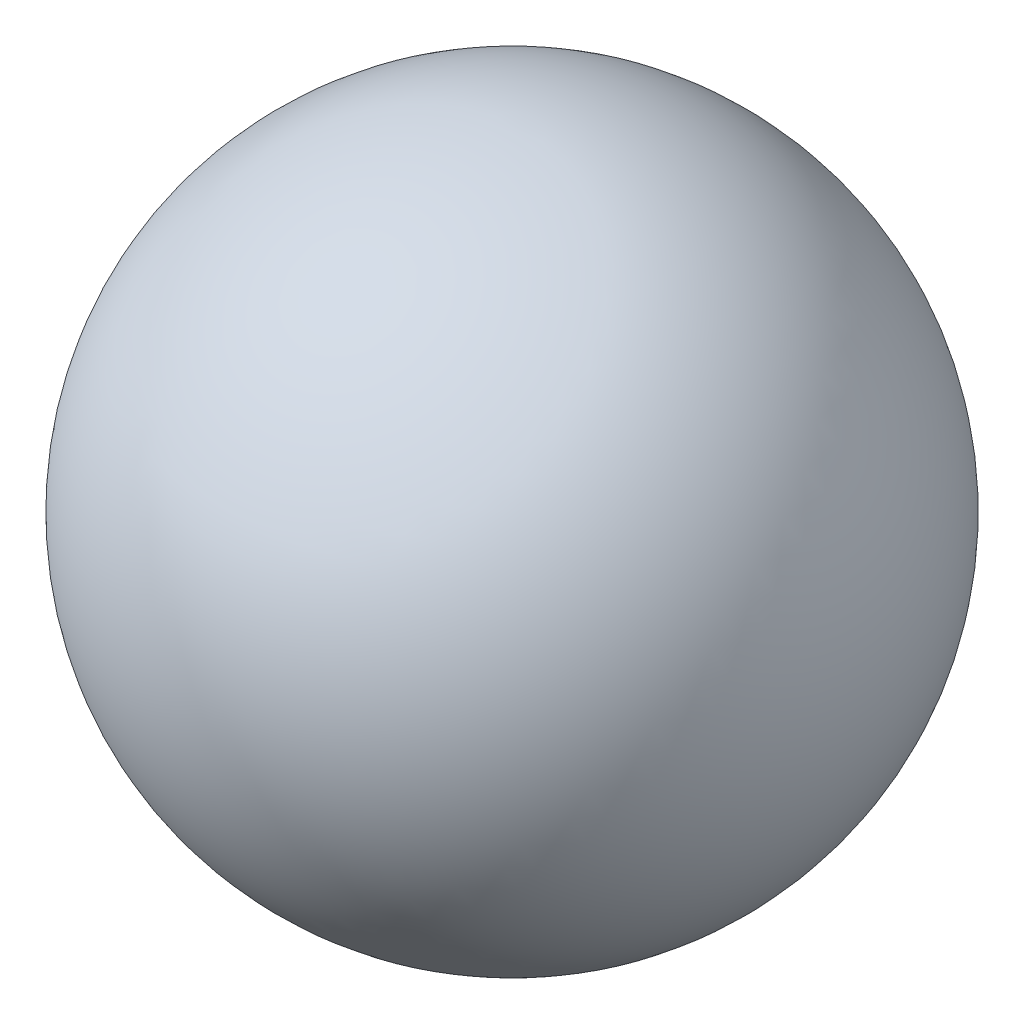
SolidWorks part; units mm, degrees
ref_plane "Alzado" through (0, 0, 0) normal (0, 0, 1) x (1, 0, 0)
ref_plane "Planta" through (0, 0, 0) normal (0, 1, 0) x (1, 0, 0)
ref_plane "Vista lateral" through (0, 0, 0) normal (1, 0, 0) x (0, 0, -1)
sketch "Croquis1" plane through (0, 0, 0) normal (0, 0, 1) x (1, 0, 0)
  line L0 (0, 6.75) -> (0, -6.75)
  arc A0 (0, -6.75) -> (0, 6.75) centre (0, 0) ccw
  dimension "D1" = 13.5
revolve "Revolución1" add sketch "Croquis1" angle 360 about L0
ref_plane "Plano1" through (0, -6.75, 0) normal (0, -1, 0) x (-1, 0, 0)
